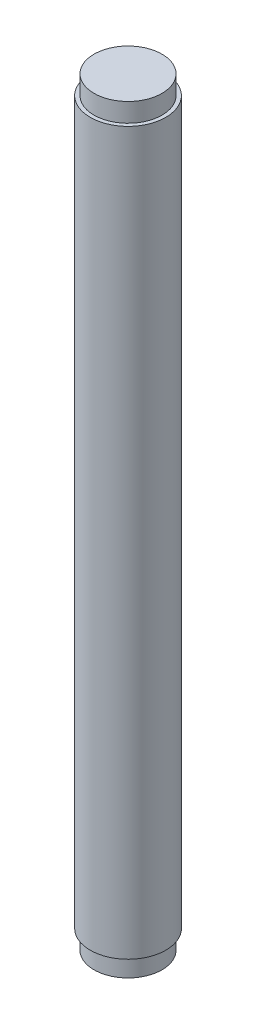
SolidWorks part; units mm, degrees
ref_plane "Front Plane" through (0, 0, 0) normal (0, 0, 1) x (1, 0, 0)
ref_plane "Top Plane" through (0, 0, 0) normal (0, 1, 0) x (1, 0, 0)
ref_plane "Right Plane" through (0, 0, 0) normal (1, 0, 0) x (0, 0, -1)
sketch "Sketch1" plane through (0, 0, 0) normal (0, 1, 0) x (1, 0, 0)
  circle A0 centre (0, 0) radius 5
extrude "Boss-Extrude1" add sketch "Sketch1" along normal blind 100.5
sketch "Sketch24" plane through (0, 0, 0) normal (0, -1, 0) x (-1, 0, 0)
  circle A0 centre (0, 0) radius 5
  circle A1 centre (0, 0) radius 4.5
  dimension "D1" = 0.5
extrude "Cut-Extrude3" cut sketch "Sketch24" against normal blind 2.5
sketch "Sketch25" plane through (0, 100.5, 0) normal (0, 1, 0) x (1, 0, 0)
  circle A0 centre (0, 0) radius 5
  circle A1 centre (0, 0) radius 4.5
  dimension "D1" = 0.5
extrude "Cut-Extrude4" cut sketch "Sketch25" against normal blind 2.5
